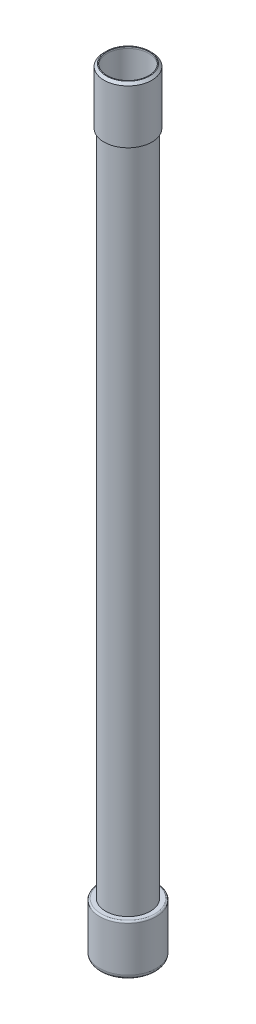
SolidWorks part; units mm, degrees
ref_plane "Front Plane" through (0, 0, 0) normal (0, 0, 1) x (1, 0, 0)
ref_plane "Top Plane" through (0, 0, 0) normal (0, 1, 0) x (1, 0, 0)
ref_plane "Right Plane" through (0, 0, 0) normal (1, 0, 0) x (0, 0, -1)
sketch "Sketch1" plane through (0, 0, 0) normal (0, 1, 0) x (1, 0, 0)
  circle A0 centre (0, 0) radius 14
  circle A1 centre (0, 0) radius 13
  dimension "D1" = 28
  dimension "D2" = 1
extrude "Extrude1" add sketch "Sketch1" along normal mid plane 480
sketch "Sketch2" plane through (0, 0, 0) normal (0, 0, 1) x (1, 0, 0)
  line L0 (0, -191.8545) -> (0, -266.8259) construction
  line L1 (13, -211) -> (17.75, -211)
  line L2 (17.75, -211) -> (17.75, -242)
  line L3 (-14, -240) -> (14, -240) construction
  line L4 (0, -246) -> (-44.4365, -246) construction
  line L6 (13, -240) -> (13, 240) construction
  line L7 (13, -240) -> (13, -211)
  line L8 (-13, -240) -> (13, -240) construction
  line L9 (0, -240) -> (13, -240)
  line L10 (0, -240) -> (0, -246)
  arc A0 (0, -246) -> (17.75, -242) centre (0, -204.6172) ccw
  dimension "D1" = 35.5
  dimension "D2" = 6
  dimension "D3" = 2
  dimension "D4" = 35
revolve "Revolve1" add sketch "Sketch2" angle 360 about L0
fillet "Fillet1" radius 3 1 edges at (0, -242, 17.75)
fillet "Fillet2" radius 1 1 edges at (0, -211, 17.75)
sketch "Sketch3" plane through (0, 0, 0) normal (0, 0, 1) x (1, 0, 0)
  line L0 (0, 250.6488) -> (0, 200.6455) construction
  line L1 (15, 241) -> (15, 206)
  line L2 (14, -240) -> (14, 240) construction
  line L3 (14, 206) -> (14, 240)
  line L4 (15, 206) -> (14, 206)
  line L5 (13, 241) -> (15, 241)
  line L6 (13, 240) -> (-13, 240) construction
  line L7 (13, -240) -> (13, 240) construction
  line L8 (13, 240) -> (13, 241)
  line L9 (14, 240) -> (-14, 240) construction
  line L10 (14, 240) -> (13, 240)
  dimension "D1" = 30
  dimension "D2" = 35
  dimension "D3" = 1
revolve "Revolve2" add sketch "Sketch3" angle 360 about L0
chamfer "Chamfer1" distance 1.5 angle 45 1 edges at (0, 241, 15)
sketch "Sketch4" plane through (0, 0, 0) normal (0, 0, 1) x (1, 0, 0)
  arc A0 (-15.9029, -242.8224) -> (15.9029, -242.8224) centre (0, -204.6172) ccw construction
  point P0 (0, -246)
